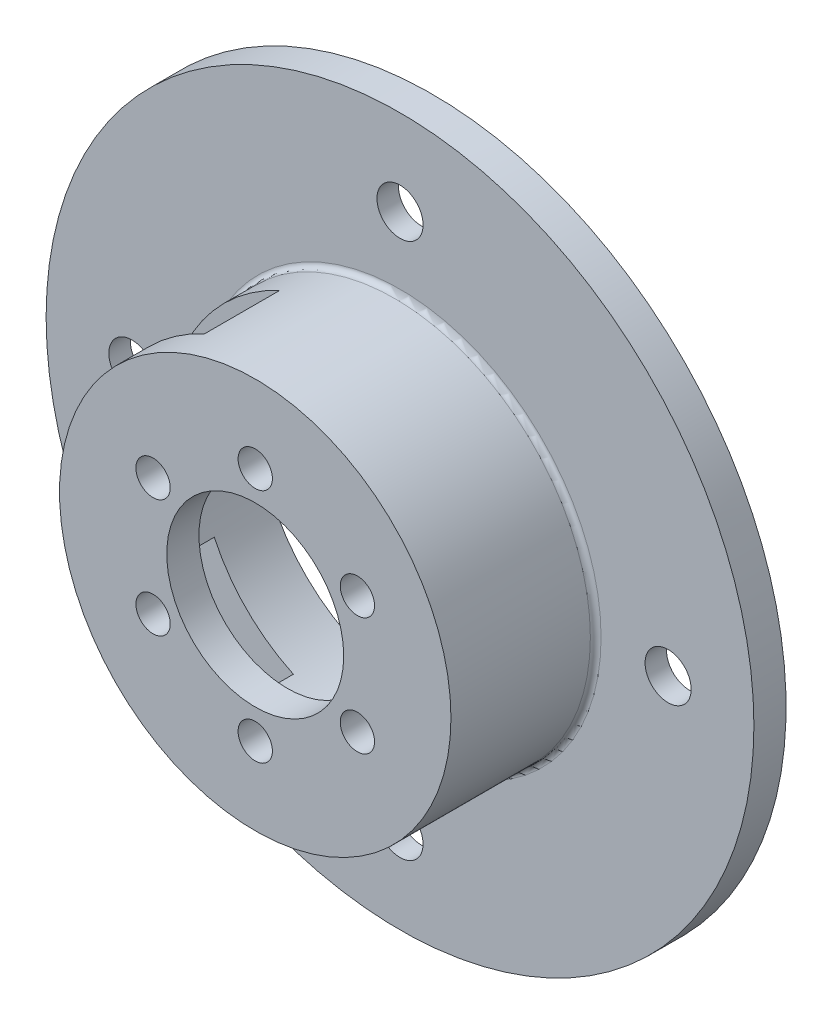
SolidWorks part; units mm, degrees
material "1060 Alloy"
ref_plane "Front Plane" through (0, 0, 0) normal (0, 0, 1) x (1, 0, 0)
ref_plane "Top Plane" through (0, 0, 0) normal (0, 1, 0) x (1, 0, 0)
ref_plane "Right Plane" through (0, 0, 0) normal (1, 0, 0) x (0, 0, -1)
sketch "Sketch1" plane through (0, 0, 0) normal (0, 0, 1) x (1, 0, 0)
  circle A0 centre (0, 0) radius 33
  circle A1 centre (0, 0) radius 15.25
  dimension "D1" = 66
  dimension "D2" = 30.5
extrude "Boss-Extrude1" add sketch "Sketch1" along normal blind 4
sketch "Sketch2" plane through (0, 0, 4) normal (0, 0, 1) x (1, 0, 0)
  circle A0 centre (0, 0) radius 15.25
  circle A1 centre (0, 0) radius 18.25
  dimension "D1" = 36.5
  dimension "D2" = 30.5
extrude "Boss-Extrude2" add sketch "Sketch2" along normal blind 13.5
sketch "Sketch3" plane through (0, 0, 17.5) normal (0, 0, 1) x (1, 0, 0)
  circle A0 centre (0, 0) radius 18.25
  circle A1 centre (0, 0) radius 8.25
  dimension "D1" = 16.5
  dimension "D2" = 36.5
extrude "Boss-Extrude3" add sketch "Sketch3" against normal blind 3
hole_wizard "M3 Clearance Hole2" positions "Sketch5" profile "Sketch4" hole size "M3" standard "ISO" end condition through all
sketch "Sketch5" plane through (0, 0, 17.5) normal (0, 0, 1) x (1, 0, 0)
  point P0 (0, 11)
  point P9 (9.5263, 5.5)
  point P10 (9.5263, -5.5)
  point P11 (0, -11)
  point P12 (-9.5263, -5.5)
  point P13 (-9.5263, 5.5)
  point P14 (0, 0)
  dimension "D1" = 11
  dimension "D2" = 6
sketch "Sketch4" plane through (0, 11, 17.5) normal (1, 0, 0) x (0, -1, 0)
  line L0 (0, 0) -> (0, 17.5)
  line L1 (0, 17.5) -> (1.6, 17.5)
  line L2 (1.6, 17.5) -> (1.6, 0)
  line L5 (1.6, 0) -> (0, 0)
  line L11 (0, -6.35) -> (0, 107.95) construction
  dimension "Thru Hole Dia." = 3.2
  dimension "Thru Hole Depth" = 17.5
hole_wizard "M3 Clearance Hole1" positions "Sketch7" profile "Sketch6" hole size "M3" standard "ISO"
sketch "Sketch7" plane through (0, 0, 3) normal (0, 0, 1) x (1, 0, 0)
  point P0 (0, 21)
  point P9 (21, 0)
  point P10 (0, -21)
  point P11 (-21, 0)
  point P12 (0, 0)
  dimension "D1" = 21
  dimension "D2" = 4
sketch "Sketch6" plane through (0, 21, 3) normal (1, 0, 0) x (0, -1, 0)
  line L0 (0, 0) -> (0, 3)
  line L1 (0, 3) -> (1.6, 3)
  line L2 (1.6, 3) -> (1.6, 0)
  line L5 (1.6, 0) -> (0, 0)
  line L11 (0, -6.35) -> (0, 107.95) construction
  dimension "Thru Hole Dia." = 3.2
  dimension "Thru Hole Depth" = 3
ref_plane "Plane1" through (0, 0, 14.5) normal (0, 0, 1) x (1, 0, 0)
sketch "Sketch9" plane through (0, 0, 14.5) normal (0, 0, 1) x (1, 0, 0)
  line L0 (0, 0) -> (9.8995, 9.8995)
  line L1 (0, 0) -> (-7.7128, -16.5401)
  line L2 (0, 0) -> (-16.5401, -7.7128)
  line L3 (0, 0) -> (-7.7128, 16.5401)
  line L4 (0, 0) -> (-16.5401, 7.7128)
  line L5 (0, 0) -> (16.5401, 7.7128)
  line L6 (0, 0) -> (7.7128, 16.5401)
  line L7 (0, 0) -> (7.7128, -16.5401)
  line L8 (0, 0) -> (16.5401, -7.7128)
  circle A0 centre (0, 0) radius 18.25
  circle A1 centre (0, 0) radius 14
  point P8 (0, 0)
  point P10 (0, 0)
  point P11 (0, 0)
  point P19 (0, 0)
  dimension "D3" = 4
  dimension "D2" = 2
  dimension "D1" = 2
extrude "Cut-Extrude2" cut sketch "Sketch9" against normal blind 7 contours A1 L3 A0 L4 | A1 L2 A0 L1
sketch "Sketch10" plane through (0, 0, 0) normal (0, 0, -1) x (-1, 0, 0)
  circle A1 centre (0, 0) radius 35
extrude "Cut-Extrude3" cut sketch "Sketch10" against normal blind 1
hole_wizard "M4 Clearance Hole1" positions "Sketch12" profile "Sketch11" hole size "M4" standard "ISO" end condition through all
sketch "Sketch12" plane through (0, 0, 4) normal (0, 0, 1) x (1, 0, 0)
  point P0 (0, 25)
  point P9 (25, 0)
  point P10 (0, -25)
  point P11 (-25, 0)
  point P12 (0, 0)
  dimension "D1" = 25
  dimension "D2" = 4
sketch "Sketch11" plane through (0, 25, 4) normal (1, 0, 0) x (0, -1, 0)
  line L0 (0, 0) -> (0, 3)
  line L1 (0, 3) -> (2.15, 3)
  line L2 (2.15, 3) -> (2.15, 0)
  line L5 (2.15, 0) -> (0, 0)
  line L11 (0, -6.35) -> (0, 107.95) construction
  dimension "Thru Hole Dia." = 4.3
  dimension "Thru Hole Depth" = 3
fillet "Fillet1" radius 0.5 2 edges at (-15.25, 0, 14.5) (18.25, 0, 4)
fillet "Fillet2" radius 0.5 1 edges at (-15.25, 0, 1)
sketch "Sketch13" plane through (0, 0, 1) normal (0, 0, -1) x (-1, 0, 0)
  circle A0 centre (0, 0) radius 30
  dimension "D1" = 60
extrude "Cut-Extrude4" cut sketch "Sketch13" against normal blind 1
fillet "Fillet3" radius 0.5 1 edges at (-30, 0, 2)
